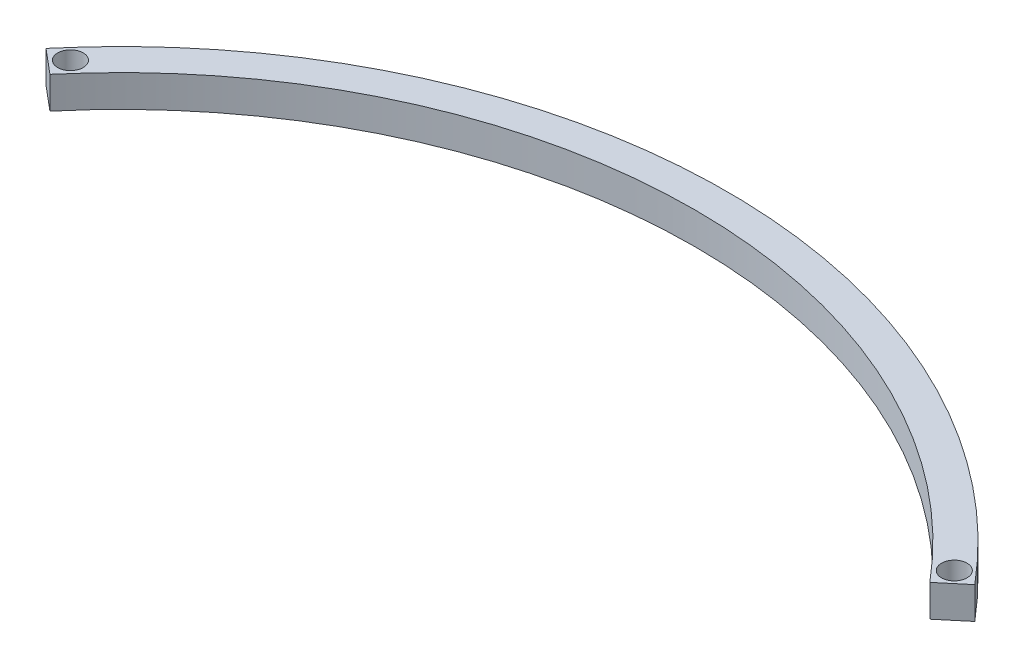
SolidWorks part; units mm, degrees
ref_plane "Front Plane" through (0, 0, 0) normal (0, 0, 1) x (1, 0, 0)
ref_plane "Top Plane" through (0, 0, 0) normal (0, 1, 0) x (1, 0, 0)
ref_plane "Right Plane" through (0, 0, 0) normal (1, 0, 0) x (0, 0, -1)
sketch "Sketch1" plane through (0, 0, 0) normal (0, 1, 0) x (1, 0, 0)
  line L0 (-145.5484, 122.1296) -> (-137.888, 115.7018)
  line L1 (145.5484, 122.1296) -> (137.888, 115.7018)
  line L2 (-137.888, 115.7018) -> (0, 0) construction
  line L3 (0, 0) -> (137.888, 115.7018) construction
  line L4 (0, 0) -> (0, 180) construction
  line L5 (-141.7182, 118.9157) -> (-138.5043, 122.7459) construction
  arc A0 (-145.5484, 122.1296) -> (145.5484, 122.1296) centre (0, 0) cw
  arc A1 (-137.888, 115.7018) -> (137.888, 115.7018) centre (0, 0) cw
  circle A2 centre (-138.5043, 122.7459) radius 4
  circle A4 centre (138.5043, 122.7459) radius 4
  dimension "D1" = 10
  dimension "D2" = 180
  dimension "D4" = 8
  dimension "D3" = 100
  dimension "D5" = 5
extrude "Boss-Extrude1" add sketch "Sketch1" along normal mid plane 10
